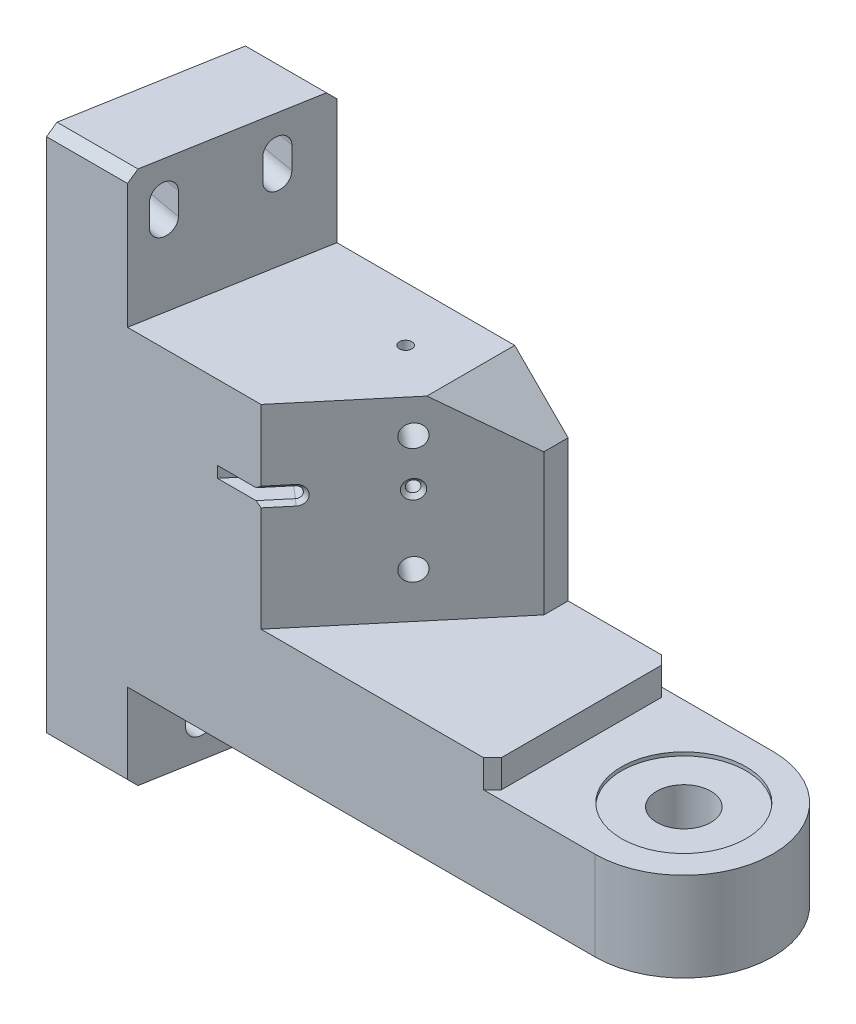
SolidWorks part; units mm, degrees
material "6061-T6 Al"
ref_plane "Front" through (0, 0, 0) normal (0, 0, 1) x (1, 0, 0)
ref_plane "Top" through (0, 0, 0) normal (0, 1, 0) x (1, 0, 0)
ref_plane "Right" through (0, 0, 0) normal (1, 0, 0) x (0, 0, -1)
sketch "Sketch1" plane through (0, 0, 0) normal (0, 1, 0) x (1, 0, 0)
  line L0 (-156.464, 0) -> (25.4, 0) construction
  line L1 (-156.464, 25.4) -> (25.4, 25.4)
  line L2 (-156.464, 25.4) -> (-156.464, -25.4)
  line L3 (-156.464, -25.4) -> (25.4, -25.4)
  line L4 (25.4, 25.4) -> (25.4, -25.4)
  dimension "D1" = 25.4
  dimension "D2" = 181.864
  dimension "D3" = 50.8
extrude "Extrude1" add sketch "Sketch1" along normal blind 152.4
sketch "Sketch2" plane through (0, 152.4, 0) normal (0, 1, 0) x (1, 0, 0)
  line L0 (-156.464, -25.4) -> (-156.464, 25.4)
  line L1 (-156.464, 25.4) -> (-147.5066, 25.4)
  line L2 (25.4, 25.4) -> (-156.464, 25.4) construction
  line L3 (-147.5066, 25.4) -> (-156.464, -25.4)
  dimension "D1" = 10
extrude "Extrude2" cut sketch "Sketch2" against normal through all
sketch "Sketch3" plane through (0, 152.4, 0) normal (0, 1, 0) x (1, 0, 0)
  line L0 (25.4, -25.4) -> (25.4, 25.4) construction
  line L1 (-156.464, -25.4) -> (25.4, -25.4) construction
  line L2 (25.4, 25.4) -> (-147.5066, 25.4) construction
  line L3 (25.4, -25.4) -> (25.4, 25.4)
  line L4 (-133.35, -25.4) -> (25.4, -25.4)
  line L5 (25.4, 25.4) -> (-124.3926, 25.4)
  line L6 (-124.3926, 25.4) -> (-133.35, -25.4)
  line L7 (-156.464, -25.4) -> (-147.5066, 25.4) construction
  dimension "D1" = 133.35
extrude "Extrude3" cut sketch "Sketch3" against normal blind 38.1
sketch "Sketch4" plane through (0, 114.3, 0) normal (0, 1, 0) x (1, 0, 0)
  line L1 (-133.35, -25.4) -> (25.4, -25.4) construction
  line L2 (25.4, 25.4) -> (-124.3926, 25.4) construction
  line L3 (25.4, -25.4) -> (25.4, 25.4) construction
  line L4 (25.4, -25.4) -> (-95.25, -25.4)
  line L5 (-58.42, 25.4) -> (25.4, 25.4)
  line L6 (-58.42, 25.4) -> (-58.42, 18.4923)
  line L7 (-58.42, 18.4923) -> (-95.25, -25.4)
  line L8 (25.4, -25.4) -> (25.4, 25.4)
  dimension "D1" = 130
  dimension "D2" = 58.42
  dimension "D3" = 95.25
extrude "Extrude4" cut sketch "Sketch4" against normal blind 55.5498
sketch "Sketch5" plane through (0, 58.7502, 0) normal (0, 1, 0) x (1, 0, 0)
  line L0 (-95.25, -25.4) -> (25.4, -25.4) construction
  line L1 (25.4, -25.4) -> (25.4, 25.4) construction
  line L2 (25.4, 25.4) -> (-58.42, 25.4) construction
  line L3 (-29.21, -25.4) -> (25.4, -25.4)
  line L4 (25.4, -25.4) -> (25.4, 25.4)
  line L5 (25.4, 25.4) -> (-29.21, 25.4)
  line L6 (-29.21, 25.4) -> (-29.21, -25.4)
  dimension "D1" = 29.21
extrude "Extrude5" cut sketch "Sketch5" against normal blind 7.9502
sketch "Sketch6" plane through (0, 0, 0) normal (0, -1, 0) x (1, 0, 0)
  line L0 (25.4, 25.4) -> (25.4, -25.4) construction
  line L1 (25.4, -25.4) -> (-147.5066, -25.4) construction
  line L2 (-156.464, 25.4) -> (25.4, 25.4) construction
  line L3 (25.4, 25.4) -> (25.4, -25.4)
  line L4 (25.4, -25.4) -> (-124.3926, -25.4)
  line L5 (-133.35, 25.4) -> (25.4, 25.4)
  line L7 (-124.3926, -25.4) -> (-133.35, 25.4)
extrude "Extrude6" cut sketch "Sketch6" against normal blind 25.4
sketch "Sketch7" plane through (-124.9853, 0, -22.0383) normal (0.9848, 0, 0.1736) x (0.1736, 0, -0.9848)
  line L0 (-39.2044, 142.9766) -> (-39.2044, 136.6266) construction
  line L1 (-35.6357, 142.9766) -> (-35.6357, 136.6266)
  line L2 (-42.7731, 142.9766) -> (-42.7731, 136.6266)
  line L3 (-48.1701, 0) -> (3.4136, 0) construction
  line L4 (-52.1838, 152.4) -> (-52.1838, 0) construction
  arc A0 (-35.6357, 142.9766) -> (-42.7731, 142.9766) centre (-39.2044, 142.9766) ccw
  arc A1 (-42.7731, 136.6266) -> (-35.6357, 136.6266) centre (-39.2044, 136.6266) ccw
  circle A2 centre (-39.2044, 139.8016) radius 3.5687 construction
  point P2 (-39.2044, 139.8016)
  dimension "D1" = 7.1374
  dimension "D2" = 6.35
  dimension "D3" = 139.8016
  dimension "D4" = 12.9794
extrude "Extrude7" cut sketch "Sketch7" against normal through all
pattern_linear "LPattern1" count 2 spacing 127 along (0, -1, 0) count 2 spacing 27.94 along (0.1736, 0, -0.9848) skipping (1, 0) of "Extrude7"
hole_wizard "1/4-20 Tapped Hole1" positions "Sketch9" profile "Sketch8" tap size "1/4-20" standard "Ansi Inch"
sketch "Sketch9" plane through (-43.3879, 0, -36.4068) normal (0.766, 0, 0.6428) x (0.6428, 0, -0.766)
  line L0 (-3.1307, 25.4) -> (-105.1733, 25.4) construction
  line L4 (-80.683, 58.7502) -> (-80.683, 114.3) construction
  point P0 (-49.822, 104.648)
  point P2 (-49.822, 71.628)
  dimension "D1" = 33.02
  dimension "D2" = 46.228
  dimension "D3" = 30.861
sketch "Sketch8" plane through (-75.4129, 104.648, 1.7591) normal (0, 1, 0) x (0.6428, 0, -0.766)
  line L0 (0, 0) -> (0, 18.0438)
  line L1 (0, 18.0438) -> (2.5527, 16.51)
  line L2 (2.5527, 16.51) -> (2.5527, 12.7)
  line L3 (2.5527, 12.7) -> (3.175, 12.7)
  line L4 (3.175, 12.7) -> (3.175, 0)
  line L5 (3.175, 0) -> (0, 0)
  line L10 (0, 18.0438) -> (-2.5527, 16.51) construction
  line L11 (0, -6.35) -> (0, 107.95) construction
  dimension "Tap Drill Dia." = 5.1054
  dimension "Tap Drill Depth" = 16.51
  dimension "Thread Major Dia." = 6.35
  dimension "Thread Depth" = 12.7
  dimension "Drill Angle" = 118
sketch "Sketch19" plane through (0, 25.4, 0) normal (0, -1, 0) x (1, 0, 0)
  line L4 (25.4, 25.4) -> (-133.35, 25.4)
  line L5 (-133.35, 25.4) -> (-124.3926, -25.4)
  line L6 (-124.3926, -25.4) -> (25.4, -25.4)
  line L7 (25.4, -25.4) -> (25.4, 25.4)
  line L8 (27.94, 25.4) -> (0, 25.4)
  line L10 (0, -25.4) -> (27.94, -25.4)
  line L11 (27.94, -25.4) -> (27.94, 25.4)
  arc A0 (0, -25.4) -> (0, 25.4) centre (0, 0) ccw
  dimension "D2" = 25.4
  dimension "D3" = 27.94
  dimension "D4" = 50.8
  dimension "D1" = 0
extrude "Extrude9" cut sketch "Sketch19" against normal through all
chamfer "Chamfer1" distance 2.54 angle 45 6 edges at (-29.21, 54.7751, 25.4) (-29.21, 54.7751, -25.4) (-135.9496, 152.4, -25.4) (-135.9496, 0, -25.4) (-144.907, 0, 25.4) (-144.907, 152.4, 25.4)
chamfer "Chamfer2" distance 15.24 angle 45 1 edges at (-58.42, 114.3, -21.9461)
sketch "Sketch20" plane through (-124.9853, 0, -22.0383) normal (0.9848, 0, 0.1736) x (0.1736, 0, -0.9848)
  line L0 (-30.3144, 15.9766) -> (-30.3144, 9.6266) construction
  line L1 (-26.7457, 15.9766) -> (-26.7457, 9.6266)
  line L2 (-33.8831, 15.9766) -> (-33.8831, 9.6266)
  line L3 (-11.2644, 9.6266) -> (-30.3144, 9.6266) construction
  line L4 (-11.2644, 15.9766) -> (-30.3144, 15.9766) construction
  arc A0 (-26.7457, 15.9766) -> (-33.8831, 15.9766) centre (-30.3144, 15.9766) ccw
  arc A1 (-33.8831, 9.6266) -> (-26.7457, 9.6266) centre (-30.3144, 9.6266) ccw
  arc A2 (-14.8331, 9.6266) -> (-7.6957, 9.6266) centre (-11.2644, 9.6266) ccw construction
  point P2 (-30.3144, 12.8016)
  dimension "D1" = 19.05
extrude "Extrude10" cut sketch "Sketch20" against normal through all
hole_wizard "SCREW THRU HOLE AND CBORE" positions "Sketch22" profile "Sketch21" counterbore size "5/8" standard "Ansi Inch" end condition through all
sketch "Sketch22" plane through (0, 50.8, 0) normal (0, 1, 0) x (-1, 0, 0)
  point P0 (0, 0)
sketch "Sketch21" plane through (0, 50.8, 0) normal (1, 0, 0) x (0, 0, 1)
  line L0 (0, 0) -> (0, 50.8)
  line L1 (0, 50.8) -> (7.7343, 50.8)
  line L3 (7.7343, 50.8) -> (7.7343, 1.016)
  line L4 (7.7343, 1.016) -> (17.78, 1.016)
  line L5 (17.78, 1.016) -> (17.78, 0)
  line L7 (17.78, 0) -> (0, 0)
  line L11 (0, -6.35) -> (0, 107.95) construction
  dimension "Thru Hole Dia." = 15.4686
  dimension "Thru Hole Depth" = 50.8
  dimension "C'Bore Dia." = 35.56
  dimension "C'Bore Depth" = 1.016
hole_wizard "1/8 (0.125) Diameter Hole1" positions "Sketch25" profile "Sketch24" hole size "1/8" standard "Ansi Inch"
sketch "Sketch25" plane through (-43.3879, 0, -36.4068) normal (0.766, 0, 0.6428) x (0.6428, 0, -0.766)
  line L0 (-80.683, 58.7502) -> (-80.683, 114.3) construction
  circle A0 centre (-49.822, 104.648) radius 2.5527 construction
  point P0 (-49.784, 91.4126)
  dimension "D1" = 13.2354
  dimension "D2" = 30.899
sketch "Sketch24" plane through (-75.3885, 91.4126, 1.73) normal (0, 1, 0) x (0.6428, 0, -0.766)
  line L0 (0, 0) -> (0, 10.4834)
  line L1 (0, 10.4834) -> (1.5951, 9.525)
  line L2 (1.5951, 9.525) -> (1.5951, 1.0719)
  line L3 (1.5951, 1.0719) -> (2.667, 0)
  line L5 (2.667, 0) -> (0, 0)
  line L6 (-1.5951, 1.0719) -> (-2.667, 0) construction
  line L10 (0, 10.4834) -> (-1.5951, 9.525) construction
  line L11 (0, -6.35) -> (0, 107.95) construction
  dimension "Hole Dia." = 3.1902
  dimension "Hole Depth" = 9.525
  dimension "Near C'Sink Dia." = 5.334
  dimension "Near C'Sink Angle" = 90
  dimension "Drill Angle" = 118
sketch "Sketch26" plane through (-43.3879, 0, -36.4068) normal (0.766, 0, 0.6428) x (0.6428, 0, -0.766)
  line L0 (-73.6092, 91.4126) -> (-92.6592, 91.4126) construction
  line L1 (-73.6092, 89.8175) -> (-92.6592, 89.8175)
  line L2 (-73.6092, 93.0077) -> (-92.6592, 93.0077)
  line L4 (-49.784, 91.4126) -> (-73.6092, 91.4126) construction
  arc A0 (-73.6092, 89.8175) -> (-73.6092, 93.0077) centre (-73.6092, 91.4126) ccw
  arc A1 (-92.6592, 93.0077) -> (-92.6592, 89.8175) centre (-92.6592, 91.4126) ccw
  circle A2 centre (-49.784, 91.4126) radius 1.5951 construction
  point P2 (-83.1342, 91.4126)
  dimension "D1" = 23.8252
  dimension "D2" = 19.05
extrude "Cut-Extrude1" cut sketch "Sketch26" against normal blind 9.525
chamfer "Chamfer3" distance 1.0795 angle 45 3 edges at (-92.9765, 89.8175, 22.6906) (-92.9765, 93.0077, 22.6906) (-89.6777, 91.4126, 18.7592)
hole_wizard "9/64 (0.14063) Diameter Hole1" positions "Sketch28" profile "Sketch29" hole size "9/64" standard "Ansi Inch"
sketch "Sketch28" plane through (0, 114.3, 0) normal (0, 1, 0) x (-1, 0, 0)
  point P0 (89.2353, -9.8392)
sketch "Sketch29" plane through (-89.2353, 114.3, -9.8392) normal (1, 0, 0) x (0, 0, 1)
  line L0 (0, 0) -> (0, 43.18)
  line L1 (0, 43.18) -> (1.786, 43.18)
  line L2 (1.786, 43.18) -> (1.786, 0)
  line L5 (1.786, 0) -> (0, 0)
  line L10 (0, 43.18) -> (-1.786, 43.18) construction
  line L11 (0, -6.35) -> (0, 107.95) construction
  dimension "Hole Dia." = 3.572
  dimension "Hole Depth" = 43.18
  dimension "Drill Angle" = 180
hole_wizard "1/16 (0.0625) Diameter Hole1" positions "Sketch31" profile "Sketch32" hole size "1/16" standard "Ansi Inch"
sketch "Sketch31" plane through (-43.3879, 0, -36.4068) normal (0.766, 0, 0.6428) x (0.6428, 0, -0.766)
  point P0 (-49.784, 91.4126)
sketch "Sketch32" plane through (-75.3885, 91.4126, 1.73) normal (0, 1, 0) x (0.6428, 0, -0.766)
  line L0 (0, 0) -> (0, 16.51)
  line L1 (0, 16.51) -> (0.7937, 16.51)
  line L2 (0.7937, 16.51) -> (0.7937, 0)
  line L5 (0.7937, 0) -> (0, 0)
  line L10 (0, 16.51) -> (-0.7938, 16.51) construction
  line L11 (0, -6.35) -> (0, 107.95) construction
  dimension "Hole Dia." = 1.5875
  dimension "Hole Depth" = 16.51
  dimension "Drill Angle" = 180
